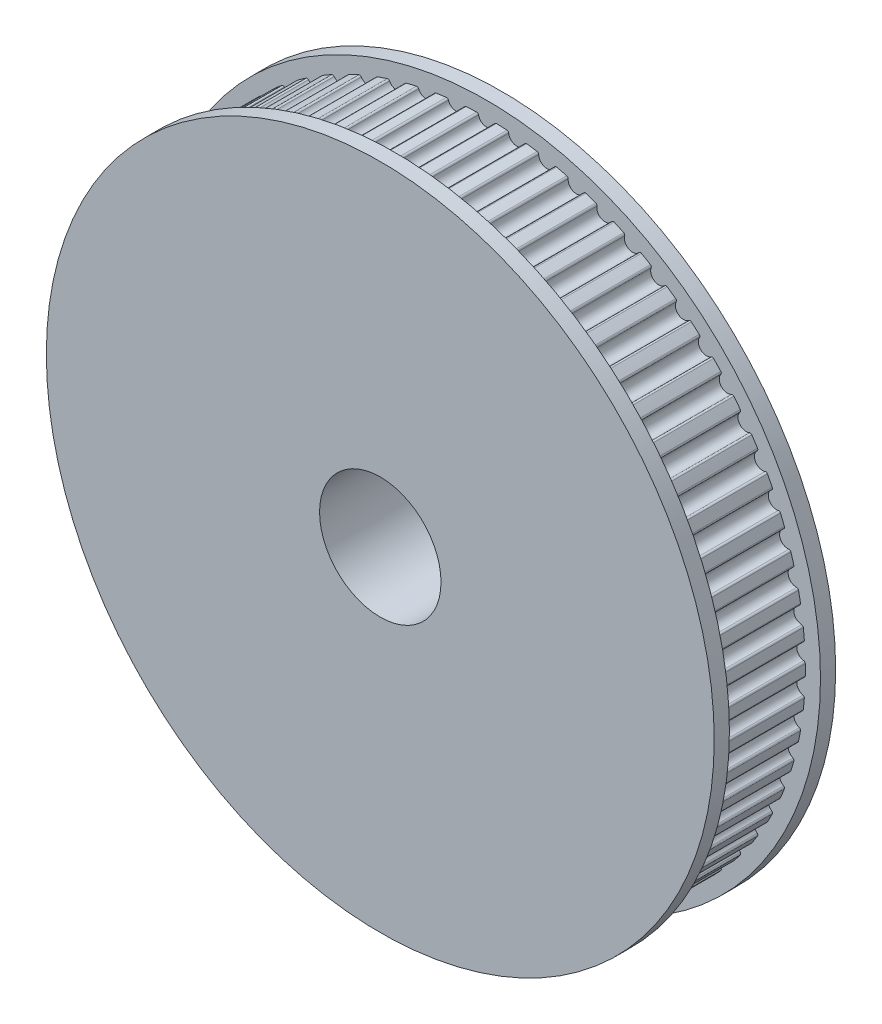
SolidWorks part; units mm, degrees
material "Plain Carbon Steel"
ref_plane "Front Plane" through (0, 0, 0) normal (0, 0, 1) x (1, 0, 0)
ref_plane "Top Plane" through (0, 0, 0) normal (0, 1, 0) x (1, 0, 0)
ref_plane "Right Plane" through (0, 0, 0) normal (1, 0, 0) x (0, 0, -1)
sketch "Sketch1" plane through (0, 0, 0) normal (0, 0, 1) x (1, 0, 0)
  circle A0 centre (0, 0) radius 4
  arc A1 (-0.655, 20.9898) -> (0.655, 20.9898) centre (0, 0) ccw
  arc A2 (-0.5287, 20.8902) -> (0.5287, 20.8902) centre (0, 21) ccw
  arc A3 (0.5287, 20.8902) -> (0.655, 20.9898) centre (0.6511, 20.8648) cw
  arc A4 (-0.5287, 20.8902) -> (-0.655, 20.9898) centre (-0.6511, 20.8648) ccw
  arc A5 (1.3432, 20.957) -> (2.6473, 20.8325) centre (0, 0) ccw
  arc A6 (1.4594, 20.8459) -> (1.3432, 20.957) centre (1.3352, 20.8323) ccw
  arc A7 (1.4594, 20.8459) -> (2.5121, 20.7454) centre (1.9962, 20.9049) ccw
  arc A8 (2.5121, 20.7454) -> (2.6473, 20.8325) centre (2.6315, 20.7085) cw
  arc A9 (3.3292, 20.7344) -> (4.6155, 20.4865) centre (0, 0) ccw
  arc A10 (3.4343, 20.6128) -> (3.3292, 20.7344) centre (3.3093, 20.611) ccw
  arc A11 (3.4343, 20.6128) -> (4.4727, 20.4127) centre (3.9743, 20.6205) ccw
  arc A12 (4.4727, 20.4127) -> (4.6155, 20.4865) centre (4.5881, 20.3646) cw
  arc A13 (5.285, 20.3241) -> (6.542, 19.955) centre (0, 0) ccw
  arc A14 (5.3782, 20.193) -> (5.285, 20.3241) centre (5.2536, 20.2031) ccw
  arc A15 (5.3782, 20.193) -> (6.3928, 19.8951) centre (5.9164, 20.1494) ccw
  arc A16 (6.3928, 19.8951) -> (6.542, 19.955) centre (6.5031, 19.8362) cw
  arc A17 (7.193, 19.7297) -> (8.4092, 19.2428) centre (0, 0) ccw
  arc A18 (7.2733, 19.5903) -> (7.193, 19.7297) centre (7.1502, 19.6122) ccw
  arc A19 (7.2733, 19.5903) -> (8.255, 19.1973) centre (7.8049, 19.4957) ccw
  arc A20 (8.255, 19.1973) -> (8.4092, 19.2428) centre (8.3592, 19.1283) cw
  arc A21 (9.0359, 18.9566) -> (10.2003, 18.3563) centre (0, 0) ccw
  arc A22 (9.1025, 18.8103) -> (9.0359, 18.9566) centre (8.9821, 18.8438) ccw
  arc A23 (9.1025, 18.8103) -> (10.0424, 18.3257) centre (9.6228, 18.6655) ccw
  arc A24 (10.0424, 18.3257) -> (10.2003, 18.3563) centre (10.1396, 18.2471) cw
  arc A25 (10.7969, 18.0119) -> (11.899, 17.3036) centre (0, 0) ccw
  arc A26 (10.8493, 17.8598) -> (10.7969, 18.0119) centre (10.7326, 17.9046) ccw
  arc A27 (10.8493, 17.8598) -> (11.7389, 17.2881) centre (11.3535, 17.6663) ccw
  arc A28 (11.7389, 17.2881) -> (11.899, 17.3036) centre (11.8281, 17.2006) cw
  arc A29 (12.4601, 16.904) -> (13.4899, 16.0942) centre (0, 0) ccw
  arc A30 (12.4979, 16.7477) -> (12.4601, 16.904) centre (12.386, 16.8034) ccw
  arc A31 (12.4979, 16.7477) -> (13.3291, 16.094) centre (12.9813, 16.5071) ccw
  arc A32 (13.3291, 16.094) -> (13.4899, 16.0942) centre (13.4096, 15.9984) cw
  arc A33 (14.0105, 15.643) -> (14.9587, 14.739) centre (0, 0) ccw
  arc A34 (14.0333, 15.4838) -> (14.0105, 15.643) centre (13.9272, 15.5499) ccw
  arc A35 (14.0333, 15.4838) -> (14.7986, 14.7541) centre (14.4917, 15.1984) ccw
  arc A36 (14.7986, 14.7541) -> (14.9587, 14.739) centre (14.8696, 14.6513) cw
  arc A37 (15.4341, 14.2404) -> (16.292, 13.2504) centre (0, 0) ccw
  arc A38 (15.4416, 14.0798) -> (15.4341, 14.2404) centre (15.3422, 14.1557) ccw
  arc A39 (15.4416, 14.0798) -> (16.134, 13.2806) centre (15.8707, 13.7521) ccw
  arc A40 (16.134, 13.2806) -> (16.292, 13.2504) centre (16.195, 13.1715) cw
  arc A41 (16.7178, 12.7088) -> (17.4777, 11.6417) centre (0, 0) ccw
  arc A42 (16.71, 12.5482) -> (16.7178, 12.7088) centre (16.6183, 12.6332) ccw
  arc A43 (16.71, 12.5482) -> (17.3234, 11.6868) centre (17.1061, 12.1812) ccw
  arc A44 (17.3234, 11.6868) -> (17.4777, 11.6417) centre (17.3737, 11.5724) cw
  arc A45 (17.8502, 11.0622) -> (18.5052, 9.9276) centre (0, 0) ccw
  arc A46 (17.8271, 10.903) -> (17.8502, 11.0622) centre (17.7439, 10.9963) ccw
  arc A47 (17.8271, 10.903) -> (18.3559, 9.9872) centre (18.1865, 10.5) ccw
  arc A48 (18.3559, 9.9872) -> (18.5052, 9.9276) centre (18.395, 9.8685) cw
  arc A49 (18.8209, 9.3153) -> (19.3651, 8.1236) centre (0, 0) ccw
  arc A50 (18.7828, 9.1591) -> (18.8209, 9.3153) centre (18.7088, 9.2598) ccw
  arc A51 (18.7828, 9.1591) -> (19.2221, 8.1972) centre (19.1023, 8.7237) ccw
  arc A52 (19.2221, 8.1972) -> (19.3651, 8.1236) centre (19.2498, 8.0753) cw
  arc A53 (19.6211, 7.4841) -> (20.0496, 6.2461) centre (0, 0) ccw
  arc A54 (19.5684, 7.3322) -> (19.6211, 7.4841) centre (19.5043, 7.4395) ccw
  arc A55 (19.5684, 7.3322) -> (19.9142, 6.3329) centre (19.845, 6.8684) ccw
  arc A56 (19.9142, 6.3329) -> (20.0496, 6.2461) centre (19.9303, 6.2089) cw
  arc A57 (20.2437, 5.5851) -> (20.5525, 4.312) centre (0, 0) ccw
  arc A58 (20.1767, 5.4389) -> (20.2437, 5.5851) centre (20.1232, 5.5518) ccw
  arc A59 (20.1767, 5.4389) -> (20.426, 4.4112) centre (20.408, 4.9509) ccw
  arc A60 (20.426, 4.4112) -> (20.5525, 4.312) centre (20.4302, 4.2863) cw
  arc A61 (20.6829, 3.6355) -> (20.8694, 2.3388) centre (0, 0) ccw
  arc A62 (20.6024, 3.4963) -> (20.6829, 3.6355) centre (20.5598, 3.6139) ccw
  arc A63 (20.6024, 3.4963) -> (20.7529, 2.4496) centre (20.7863, 2.9886) ccw
  arc A64 (20.7529, 2.4496) -> (20.8694, 2.3388) centre (20.7451, 2.3249) cw
  arc A65 (20.9348, 1.653) -> (20.9972, 0.3445) centre (0, 0) ccw
  arc A66 (20.8414, 1.5221) -> (20.9348, 1.653) centre (20.8102, 1.6432) ccw
  arc A67 (20.8414, 1.5221) -> (20.8917, 0.4659) centre (20.9762, 0.9992) ccw
  arc A68 (20.8917, 0.4659) -> (20.9972, 0.3445) centre (20.8722, 0.3424) cw
  arc A69 (20.9972, -0.3445) -> (20.9348, -1.653) centre (0, 0) ccw
  arc A70 (20.8917, -0.4659) -> (20.9972, -0.3445) centre (20.8722, -0.3424) ccw
  arc A71 (20.8917, -0.4659) -> (20.8414, -1.5221) centre (20.9762, -0.9992) ccw
  arc A72 (20.8414, -1.5221) -> (20.9348, -1.653) centre (20.8102, -1.6432) cw
  arc A73 (20.8694, -2.3388) -> (20.6829, -3.6355) centre (0, 0) ccw
  arc A74 (20.7529, -2.4496) -> (20.8694, -2.3388) centre (20.7451, -2.3249) ccw
  arc A75 (20.7529, -2.4496) -> (20.6024, -3.4963) centre (20.7863, -2.9886) ccw
  arc A76 (20.6024, -3.4963) -> (20.6829, -3.6355) centre (20.5598, -3.6139) cw
  arc A77 (20.5525, -4.312) -> (20.2437, -5.5851) centre (0, 0) ccw
  arc A78 (20.426, -4.4112) -> (20.5525, -4.312) centre (20.4302, -4.2863) ccw
  arc A79 (20.426, -4.4112) -> (20.1767, -5.4389) centre (20.408, -4.9509) ccw
  arc A80 (20.1767, -5.4389) -> (20.2437, -5.5851) centre (20.1232, -5.5518) cw
  arc A81 (20.0496, -6.2461) -> (19.6211, -7.4841) centre (0, 0) ccw
  arc A82 (19.9142, -6.3329) -> (20.0496, -6.2461) centre (19.9303, -6.2089) ccw
  arc A83 (19.9142, -6.3329) -> (19.5684, -7.3322) centre (19.845, -6.8684) ccw
  arc A84 (19.5684, -7.3322) -> (19.6211, -7.4841) centre (19.5043, -7.4395) cw
  arc A85 (19.3651, -8.1236) -> (18.8209, -9.3153) centre (0, 0) ccw
  arc A86 (19.2221, -8.1972) -> (19.3651, -8.1236) centre (19.2498, -8.0753) ccw
  arc A87 (19.2221, -8.1972) -> (18.7828, -9.1591) centre (19.1023, -8.7237) ccw
  arc A88 (18.7828, -9.1591) -> (18.8209, -9.3153) centre (18.7088, -9.2598) cw
  arc A89 (18.5052, -9.9276) -> (17.8502, -11.0622) centre (0, 0) ccw
  arc A90 (18.3559, -9.9872) -> (18.5052, -9.9276) centre (18.395, -9.8685) ccw
  arc A91 (18.3559, -9.9872) -> (17.8271, -10.903) centre (18.1865, -10.5) ccw
  arc A92 (17.8271, -10.903) -> (17.8502, -11.0622) centre (17.7439, -10.9963) cw
  arc A93 (17.4777, -11.6417) -> (16.7178, -12.7088) centre (0, 0) ccw
  arc A94 (17.3234, -11.6868) -> (17.4777, -11.6417) centre (17.3737, -11.5724) ccw
  arc A95 (17.3234, -11.6868) -> (16.71, -12.5482) centre (17.1061, -12.1812) ccw
  arc A96 (16.71, -12.5482) -> (16.7178, -12.7088) centre (16.6183, -12.6332) cw
  arc A97 (16.292, -13.2504) -> (15.4341, -14.2404) centre (0, 0) ccw
  arc A98 (16.134, -13.2806) -> (16.292, -13.2504) centre (16.195, -13.1715) ccw
  arc A99 (16.134, -13.2806) -> (15.4416, -14.0798) centre (15.8707, -13.7521) ccw
  arc A100 (15.4416, -14.0798) -> (15.4341, -14.2404) centre (15.3422, -14.1557) cw
  arc A101 (14.9587, -14.739) -> (14.0105, -15.643) centre (0, 0) ccw
  arc A102 (14.7986, -14.7541) -> (14.9587, -14.739) centre (14.8696, -14.6513) ccw
  arc A103 (14.7986, -14.7541) -> (14.0333, -15.4838) centre (14.4917, -15.1984) ccw
  arc A104 (14.0333, -15.4838) -> (14.0105, -15.643) centre (13.9272, -15.5499) cw
  arc A105 (13.4899, -16.0942) -> (12.4601, -16.904) centre (0, 0) ccw
  arc A106 (13.3291, -16.094) -> (13.4899, -16.0942) centre (13.4096, -15.9984) ccw
  arc A107 (13.3291, -16.094) -> (12.4979, -16.7477) centre (12.9813, -16.5071) ccw
  arc A108 (12.4979, -16.7477) -> (12.4601, -16.904) centre (12.386, -16.8034) cw
  arc A109 (11.899, -17.3036) -> (10.7969, -18.0119) centre (0, 0) ccw
  arc A110 (11.7389, -17.2881) -> (11.899, -17.3036) centre (11.8281, -17.2006) ccw
  arc A111 (11.7389, -17.2881) -> (10.8493, -17.8598) centre (11.3535, -17.6663) ccw
  arc A112 (10.8493, -17.8598) -> (10.7969, -18.0119) centre (10.7326, -17.9046) cw
  arc A113 (10.2003, -18.3563) -> (9.0359, -18.9566) centre (0, 0) ccw
  arc A114 (10.0424, -18.3257) -> (10.2003, -18.3563) centre (10.1396, -18.2471) ccw
  arc A115 (10.0424, -18.3257) -> (9.1025, -18.8103) centre (9.6228, -18.6655) ccw
  arc A116 (9.1025, -18.8103) -> (9.0359, -18.9566) centre (8.9821, -18.8438) cw
  arc A117 (8.4092, -19.2428) -> (7.193, -19.7297) centre (0, 0) ccw
  arc A118 (8.255, -19.1973) -> (8.4092, -19.2428) centre (8.3592, -19.1283) ccw
  arc A119 (8.255, -19.1973) -> (7.2733, -19.5903) centre (7.8049, -19.4957) ccw
  arc A120 (7.2733, -19.5903) -> (7.193, -19.7297) centre (7.1502, -19.6122) cw
  arc A121 (6.542, -19.955) -> (5.285, -20.3241) centre (0, 0) ccw
  arc A122 (6.3928, -19.8951) -> (6.542, -19.955) centre (6.5031, -19.8362) ccw
  arc A123 (6.3928, -19.8951) -> (5.3782, -20.193) centre (5.9164, -20.1494) ccw
  arc A124 (5.3782, -20.193) -> (5.285, -20.3241) centre (5.2536, -20.2031) cw
  arc A125 (4.6155, -20.4865) -> (3.3292, -20.7344) centre (0, 0) ccw
  arc A126 (4.4727, -20.4127) -> (4.6155, -20.4865) centre (4.5881, -20.3646) ccw
  arc A127 (4.4727, -20.4127) -> (3.4343, -20.6128) centre (3.9743, -20.6205) ccw
  arc A128 (3.4343, -20.6128) -> (3.3292, -20.7344) centre (3.3093, -20.611) cw
  arc A129 (2.6473, -20.8325) -> (1.3432, -20.957) centre (0, 0) ccw
  arc A130 (2.5121, -20.7454) -> (2.6473, -20.8325) centre (2.6315, -20.7085) ccw
  arc A131 (2.5121, -20.7454) -> (1.4594, -20.8459) centre (1.9962, -20.9049) ccw
  arc A132 (1.4594, -20.8459) -> (1.3432, -20.957) centre (1.3352, -20.8323) cw
  arc A133 (0.655, -20.9898) -> (-0.655, -20.9898) centre (0, 0) ccw
  arc A134 (0.5287, -20.8902) -> (0.655, -20.9898) centre (0.6511, -20.8648) ccw
  arc A135 (0.5287, -20.8902) -> (-0.5287, -20.8902) centre (0, -21) ccw
  arc A136 (-0.5287, -20.8902) -> (-0.655, -20.9898) centre (-0.6511, -20.8648) cw
  arc A137 (-1.3432, -20.957) -> (-2.6473, -20.8325) centre (0, 0) ccw
  arc A138 (-1.4594, -20.8459) -> (-1.3432, -20.957) centre (-1.3352, -20.8323) ccw
  arc A139 (-1.4594, -20.8459) -> (-2.5121, -20.7454) centre (-1.9962, -20.9049) ccw
  arc A140 (-2.5121, -20.7454) -> (-2.6473, -20.8325) centre (-2.6315, -20.7085) cw
  arc A141 (-3.3292, -20.7344) -> (-4.6155, -20.4865) centre (0, 0) ccw
  arc A142 (-3.4343, -20.6128) -> (-3.3292, -20.7344) centre (-3.3093, -20.611) ccw
  arc A143 (-3.4343, -20.6128) -> (-4.4727, -20.4127) centre (-3.9743, -20.6205) ccw
  arc A144 (-4.4727, -20.4127) -> (-4.6155, -20.4865) centre (-4.5881, -20.3646) cw
  arc A145 (-5.285, -20.3241) -> (-6.542, -19.955) centre (0, 0) ccw
  arc A146 (-5.3782, -20.193) -> (-5.285, -20.3241) centre (-5.2536, -20.2031) ccw
  arc A147 (-5.3782, -20.193) -> (-6.3928, -19.8951) centre (-5.9164, -20.1494) ccw
  arc A148 (-6.3928, -19.8951) -> (-6.542, -19.955) centre (-6.5031, -19.8362) cw
  arc A149 (-7.193, -19.7297) -> (-8.4092, -19.2428) centre (0, 0) ccw
  arc A150 (-7.2733, -19.5903) -> (-7.193, -19.7297) centre (-7.1502, -19.6122) ccw
  arc A151 (-7.2733, -19.5903) -> (-8.255, -19.1973) centre (-7.8049, -19.4957) ccw
  arc A152 (-8.255, -19.1973) -> (-8.4092, -19.2428) centre (-8.3592, -19.1283) cw
  arc A153 (-9.0359, -18.9566) -> (-10.2003, -18.3563) centre (0, 0) ccw
  arc A154 (-9.1025, -18.8103) -> (-9.0359, -18.9566) centre (-8.9821, -18.8438) ccw
  arc A155 (-9.1025, -18.8103) -> (-10.0424, -18.3257) centre (-9.6228, -18.6655) ccw
  arc A156 (-10.0424, -18.3257) -> (-10.2003, -18.3563) centre (-10.1396, -18.2471) cw
  arc A157 (-10.7969, -18.0119) -> (-11.899, -17.3036) centre (0, 0) ccw
  arc A158 (-10.8493, -17.8598) -> (-10.7969, -18.0119) centre (-10.7326, -17.9046) ccw
  arc A159 (-10.8493, -17.8598) -> (-11.7389, -17.2881) centre (-11.3535, -17.6663) ccw
  arc A160 (-11.7389, -17.2881) -> (-11.899, -17.3036) centre (-11.8281, -17.2006) cw
  arc A161 (-12.4601, -16.904) -> (-13.4899, -16.0942) centre (0, 0) ccw
  arc A162 (-12.4979, -16.7477) -> (-12.4601, -16.904) centre (-12.386, -16.8034) ccw
  arc A163 (-12.4979, -16.7477) -> (-13.3291, -16.094) centre (-12.9813, -16.5071) ccw
  arc A164 (-13.3291, -16.094) -> (-13.4899, -16.0942) centre (-13.4096, -15.9984) cw
  arc A165 (-14.0105, -15.643) -> (-14.9587, -14.739) centre (0, 0) ccw
  arc A166 (-14.0333, -15.4838) -> (-14.0105, -15.643) centre (-13.9272, -15.5499) ccw
  arc A167 (-14.0333, -15.4838) -> (-14.7986, -14.7541) centre (-14.4917, -15.1984) ccw
  arc A168 (-14.7986, -14.7541) -> (-14.9587, -14.739) centre (-14.8696, -14.6513) cw
  arc A169 (-15.4341, -14.2404) -> (-16.292, -13.2504) centre (0, 0) ccw
  arc A170 (-15.4416, -14.0798) -> (-15.4341, -14.2404) centre (-15.3422, -14.1557) ccw
  arc A171 (-15.4416, -14.0798) -> (-16.134, -13.2806) centre (-15.8707, -13.7521) ccw
  arc A172 (-16.134, -13.2806) -> (-16.292, -13.2504) centre (-16.195, -13.1715) cw
  arc A173 (-16.7178, -12.7088) -> (-17.4777, -11.6417) centre (0, 0) ccw
  arc A174 (-16.71, -12.5482) -> (-16.7178, -12.7088) centre (-16.6183, -12.6332) ccw
  arc A175 (-16.71, -12.5482) -> (-17.3234, -11.6868) centre (-17.1061, -12.1812) ccw
  arc A176 (-17.3234, -11.6868) -> (-17.4777, -11.6417) centre (-17.3737, -11.5724) cw
  arc A177 (-17.8502, -11.0622) -> (-18.5052, -9.9276) centre (0, 0) ccw
  arc A178 (-17.8271, -10.903) -> (-17.8502, -11.0622) centre (-17.7439, -10.9963) ccw
  arc A179 (-17.8271, -10.903) -> (-18.3559, -9.9872) centre (-18.1865, -10.5) ccw
  arc A180 (-18.3559, -9.9872) -> (-18.5052, -9.9276) centre (-18.395, -9.8685) cw
  arc A181 (-18.8209, -9.3153) -> (-19.3651, -8.1236) centre (0, 0) ccw
  arc A182 (-18.7828, -9.1591) -> (-18.8209, -9.3153) centre (-18.7088, -9.2598) ccw
  arc A183 (-18.7828, -9.1591) -> (-19.2221, -8.1972) centre (-19.1023, -8.7237) ccw
  arc A184 (-19.2221, -8.1972) -> (-19.3651, -8.1236) centre (-19.2498, -8.0753) cw
  arc A185 (-19.6211, -7.4841) -> (-20.0496, -6.2461) centre (0, 0) ccw
  arc A186 (-19.5684, -7.3322) -> (-19.6211, -7.4841) centre (-19.5043, -7.4395) ccw
  arc A187 (-19.5684, -7.3322) -> (-19.9142, -6.3329) centre (-19.845, -6.8684) ccw
  arc A188 (-19.9142, -6.3329) -> (-20.0496, -6.2461) centre (-19.9303, -6.2089) cw
  arc A189 (-20.2437, -5.5851) -> (-20.5525, -4.312) centre (0, 0) ccw
  arc A190 (-20.1767, -5.4389) -> (-20.2437, -5.5851) centre (-20.1232, -5.5518) ccw
  arc A191 (-20.1767, -5.4389) -> (-20.426, -4.4112) centre (-20.408, -4.9509) ccw
  arc A192 (-20.426, -4.4112) -> (-20.5525, -4.312) centre (-20.4302, -4.2863) cw
  arc A193 (-20.6829, -3.6355) -> (-20.8694, -2.3388) centre (0, 0) ccw
  arc A194 (-20.6024, -3.4963) -> (-20.6829, -3.6355) centre (-20.5598, -3.6139) ccw
  arc A195 (-20.6024, -3.4963) -> (-20.7529, -2.4496) centre (-20.7863, -2.9886) ccw
  arc A196 (-20.7529, -2.4496) -> (-20.8694, -2.3388) centre (-20.7451, -2.3249) cw
  arc A197 (-20.9348, -1.653) -> (-20.9972, -0.3445) centre (0, 0) ccw
  arc A198 (-20.8414, -1.5221) -> (-20.9348, -1.653) centre (-20.8102, -1.6432) ccw
  arc A199 (-20.8414, -1.5221) -> (-20.8917, -0.4659) centre (-20.9762, -0.9992) ccw
  arc A200 (-20.8917, -0.4659) -> (-20.9972, -0.3445) centre (-20.8722, -0.3424) cw
  arc A201 (-20.9972, 0.3445) -> (-20.9348, 1.653) centre (0, 0) ccw
  arc A202 (-20.8917, 0.4659) -> (-20.9972, 0.3445) centre (-20.8722, 0.3424) ccw
  arc A203 (-20.8917, 0.4659) -> (-20.8414, 1.5221) centre (-20.9762, 0.9992) ccw
  arc A204 (-20.8414, 1.5221) -> (-20.9348, 1.653) centre (-20.8102, 1.6432) cw
  arc A205 (-20.8694, 2.3388) -> (-20.6829, 3.6355) centre (0, 0) ccw
  arc A206 (-20.7529, 2.4496) -> (-20.8694, 2.3388) centre (-20.7451, 2.3249) ccw
  arc A207 (-20.7529, 2.4496) -> (-20.6024, 3.4963) centre (-20.7863, 2.9886) ccw
  arc A208 (-20.6024, 3.4963) -> (-20.6829, 3.6355) centre (-20.5598, 3.6139) cw
  arc A209 (-20.5525, 4.312) -> (-20.2437, 5.5851) centre (0, 0) ccw
  arc A210 (-20.426, 4.4112) -> (-20.5525, 4.312) centre (-20.4302, 4.2863) ccw
  arc A211 (-20.426, 4.4112) -> (-20.1767, 5.4389) centre (-20.408, 4.9509) ccw
  arc A212 (-20.1767, 5.4389) -> (-20.2437, 5.5851) centre (-20.1232, 5.5518) cw
  arc A213 (-20.0496, 6.2461) -> (-19.6211, 7.4841) centre (0, 0) ccw
  arc A214 (-19.9142, 6.3329) -> (-20.0496, 6.2461) centre (-19.9303, 6.2089) ccw
  arc A215 (-19.9142, 6.3329) -> (-19.5684, 7.3322) centre (-19.845, 6.8684) ccw
  arc A216 (-19.5684, 7.3322) -> (-19.6211, 7.4841) centre (-19.5043, 7.4395) cw
  arc A217 (-19.3651, 8.1236) -> (-18.8209, 9.3153) centre (0, 0) ccw
  arc A218 (-19.2221, 8.1972) -> (-19.3651, 8.1236) centre (-19.2498, 8.0753) ccw
  arc A219 (-19.2221, 8.1972) -> (-18.7828, 9.1591) centre (-19.1023, 8.7237) ccw
  arc A220 (-18.7828, 9.1591) -> (-18.8209, 9.3153) centre (-18.7088, 9.2598) cw
  arc A221 (-18.5052, 9.9276) -> (-17.8502, 11.0622) centre (0, 0) ccw
  arc A222 (-18.3559, 9.9872) -> (-18.5052, 9.9276) centre (-18.395, 9.8685) ccw
  arc A223 (-18.3559, 9.9872) -> (-17.8271, 10.903) centre (-18.1865, 10.5) ccw
  arc A224 (-17.8271, 10.903) -> (-17.8502, 11.0622) centre (-17.7439, 10.9963) cw
  arc A225 (-17.4777, 11.6417) -> (-16.7178, 12.7088) centre (0, 0) ccw
  arc A226 (-17.3234, 11.6868) -> (-17.4777, 11.6417) centre (-17.3737, 11.5724) ccw
  arc A227 (-17.3234, 11.6868) -> (-16.71, 12.5482) centre (-17.1061, 12.1812) ccw
  arc A228 (-16.71, 12.5482) -> (-16.7178, 12.7088) centre (-16.6183, 12.6332) cw
  arc A229 (-16.292, 13.2504) -> (-15.4341, 14.2404) centre (0, 0) ccw
  arc A230 (-16.134, 13.2806) -> (-16.292, 13.2504) centre (-16.195, 13.1715) ccw
  arc A231 (-16.134, 13.2806) -> (-15.4416, 14.0798) centre (-15.8707, 13.7521) ccw
  arc A232 (-15.4416, 14.0798) -> (-15.4341, 14.2404) centre (-15.3422, 14.1557) cw
  arc A233 (-14.9587, 14.739) -> (-14.0105, 15.643) centre (0, 0) ccw
  arc A234 (-14.7986, 14.7541) -> (-14.9587, 14.739) centre (-14.8696, 14.6513) ccw
  arc A235 (-14.7986, 14.7541) -> (-14.0333, 15.4838) centre (-14.4917, 15.1984) ccw
  arc A236 (-14.0333, 15.4838) -> (-14.0105, 15.643) centre (-13.9272, 15.5499) cw
  arc A237 (-13.4899, 16.0942) -> (-12.4601, 16.904) centre (0, 0) ccw
  arc A238 (-13.3291, 16.094) -> (-13.4899, 16.0942) centre (-13.4096, 15.9984) ccw
  arc A239 (-13.3291, 16.094) -> (-12.4979, 16.7477) centre (-12.9813, 16.5071) ccw
  arc A240 (-12.4979, 16.7477) -> (-12.4601, 16.904) centre (-12.386, 16.8034) cw
  arc A241 (-11.899, 17.3036) -> (-10.7969, 18.0119) centre (0, 0) ccw
  arc A242 (-11.7389, 17.2881) -> (-11.899, 17.3036) centre (-11.8281, 17.2006) ccw
  arc A243 (-11.7389, 17.2881) -> (-10.8493, 17.8598) centre (-11.3535, 17.6663) ccw
  arc A244 (-10.8493, 17.8598) -> (-10.7969, 18.0119) centre (-10.7326, 17.9046) cw
  arc A245 (-10.2003, 18.3563) -> (-9.0359, 18.9566) centre (0, 0) ccw
  arc A246 (-10.0424, 18.3257) -> (-10.2003, 18.3563) centre (-10.1396, 18.2471) ccw
  arc A247 (-10.0424, 18.3257) -> (-9.1025, 18.8103) centre (-9.6228, 18.6655) ccw
  arc A248 (-9.1025, 18.8103) -> (-9.0359, 18.9566) centre (-8.9821, 18.8438) cw
  arc A249 (-8.4092, 19.2428) -> (-7.193, 19.7297) centre (0, 0) ccw
  arc A250 (-8.255, 19.1973) -> (-8.4092, 19.2428) centre (-8.3592, 19.1283) ccw
  arc A251 (-8.255, 19.1973) -> (-7.2733, 19.5903) centre (-7.8049, 19.4957) ccw
  arc A252 (-7.2733, 19.5903) -> (-7.193, 19.7297) centre (-7.1502, 19.6122) cw
  arc A253 (-6.542, 19.955) -> (-5.285, 20.3241) centre (0, 0) ccw
  arc A254 (-6.3928, 19.8951) -> (-6.542, 19.955) centre (-6.5031, 19.8362) ccw
  arc A255 (-6.3928, 19.8951) -> (-5.3782, 20.193) centre (-5.9164, 20.1494) ccw
  arc A256 (-5.3782, 20.193) -> (-5.285, 20.3241) centre (-5.2536, 20.2031) cw
  arc A257 (-4.6155, 20.4865) -> (-3.3292, 20.7344) centre (0, 0) ccw
  arc A258 (-4.4727, 20.4127) -> (-4.6155, 20.4865) centre (-4.5881, 20.3646) ccw
  arc A259 (-4.4727, 20.4127) -> (-3.4343, 20.6128) centre (-3.9743, 20.6205) ccw
  arc A260 (-3.4343, 20.6128) -> (-3.3292, 20.7344) centre (-3.3093, 20.611) cw
  arc A261 (-2.6473, 20.8325) -> (-1.3432, 20.957) centre (0, 0) ccw
  arc A262 (-2.5121, 20.7454) -> (-2.6473, 20.8325) centre (-2.6315, 20.7085) ccw
  arc A263 (-2.5121, 20.7454) -> (-1.4594, 20.8459) centre (-1.9962, 20.9049) ccw
  arc A264 (-1.4594, 20.8459) -> (-1.3432, 20.957) centre (-1.3352, 20.8323) cw
  point P467 (0, 0)
  dimension "D1" = 0.125
extrude "Boss-Extrude1" add sketch "Sketch1" along normal blind 6
sketch "Sketch2" plane through (0, 0, 6) normal (0, 0, 1) x (1, 0, 0)
  circle A0 centre (0, 0) radius 21 construction
sketch "Sketch3" plane through (0, 0, 6) normal (0, 0, 1) x (1, 0, 0)
  circle A0 centre (0, 0) radius 4
  circle A1 centre (0, 0) radius 22
extrude "Boss-Extrude2" add sketch "Sketch3" along normal blind 1
sketch "Sketch4" plane through (0, 0, 0) normal (0, 0, -1) x (-1, 0, 0)
  circle A0 centre (0, 0) radius 4
  circle A1 centre (0, 0) radius 22
extrude "Boss-Extrude3" add sketch "Sketch4" along normal blind 1
